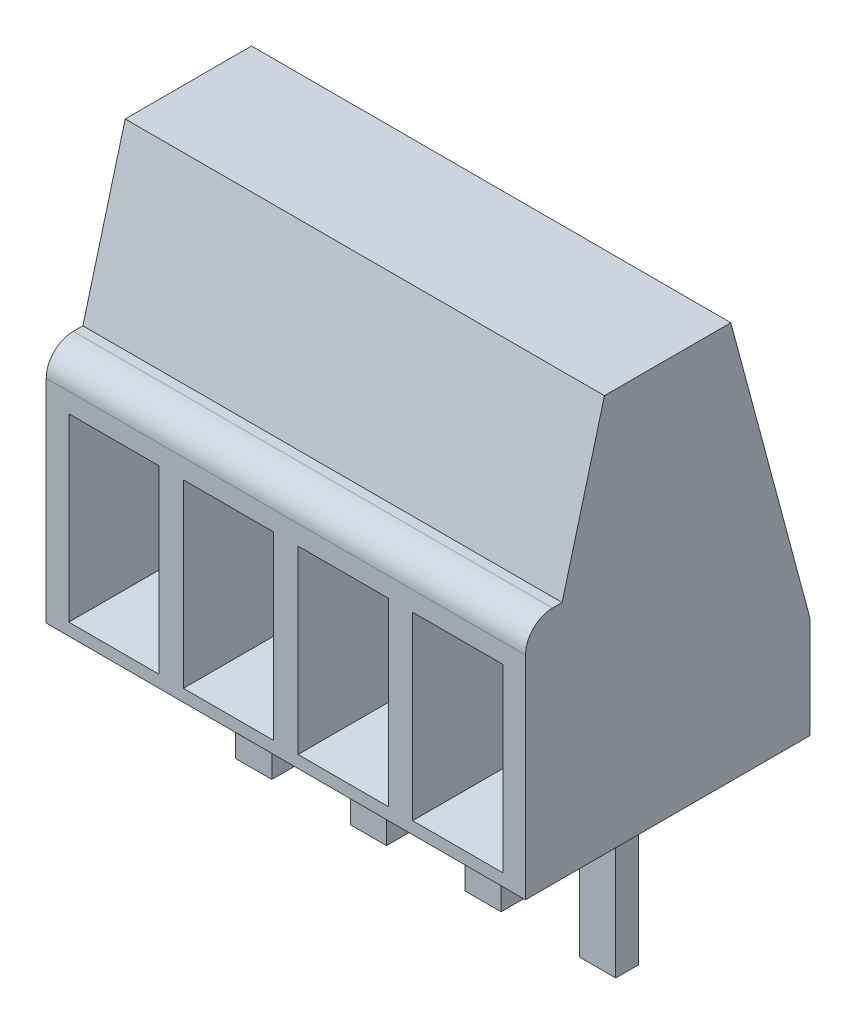
SolidWorks part; units mm, degrees
ref_plane "Front Plane" through (0, 0, 0) normal (0, 0, 1) x (1, 0, 0)
ref_plane "Top Plane" through (0, 0, 0) normal (0, 1, 0) x (1, 0, 0)
ref_plane "Right Plane" through (0, 0, 0) normal (1, 0, 0) x (0, 0, -1)
sketch "Sketch1" plane through (0, 0, 0) normal (0, 1, 0) x (1, 0, 0)
  line L1 (-5.31, -3.15) -> (5.31, -3.15)
  line L2 (-5.31, -3.15) -> (-5.31, 3.15)
  line L3 (-5.31, 3.15) -> (5.31, 3.15)
  line L4 (5.31, -3.15) -> (5.31, 3.15)
  line L5 (-5.31, -3.15) -> (5.31, 3.15) construction
  line L6 (-5.31, 3.15) -> (5.31, -3.15) construction
  point P0 (0, 0)
  dimension "D1" = 10.62
  dimension "D2" = 6.3
extrude "Boss-Extrude1" add sketch "Sketch1" along normal blind 8.8
sketch "Sketch2" plane through (0, 0, 0) normal (0, 1, 0) x (1, 0, 0)
  line L0 (5.31, 3.15) -> (-5.31, 3.15) construction
  line L1 (0.87, -0.05) -> (1.67, -0.05)
  line L2 (0.87, -0.05) -> (0.87, 0.45)
  line L3 (0.87, 0.45) -> (1.67, 0.45)
  line L4 (1.67, -0.05) -> (1.67, 0.45)
  line L5 (0.87, -0.05) -> (1.67, 0.45) construction
  line L6 (0.87, 0.45) -> (1.67, -0.05) construction
  line L7 (3.41, -0.05) -> (4.21, -0.05)
  line L8 (3.41, -0.05) -> (3.41, 0.45)
  line L9 (3.41, 0.45) -> (4.21, 0.45)
  line L10 (4.21, -0.05) -> (4.21, 0.45)
  line L11 (3.41, -0.05) -> (4.21, 0.45) construction
  line L12 (3.41, 0.45) -> (4.21, -0.05) construction
  line L13 (-0.87, -0.05) -> (-1.67, -0.05)
  line L14 (-0.87, -0.05) -> (-0.87, 0.45)
  line L15 (-0.87, 0.45) -> (-1.67, 0.45)
  line L16 (-1.67, -0.05) -> (-1.67, 0.45)
  line L17 (-0.87, -0.05) -> (-1.67, 0.45) construction
  line L18 (-0.87, 0.45) -> (-1.67, -0.05) construction
  line L19 (-3.41, -0.05) -> (-4.21, -0.05)
  line L20 (-3.41, -0.05) -> (-3.41, 0.45)
  line L21 (-3.41, 0.45) -> (-4.21, 0.45)
  line L22 (-4.21, -0.05) -> (-4.21, 0.45)
  line L23 (-3.41, -0.05) -> (-4.21, 0.45) construction
  line L24 (-3.41, 0.45) -> (-4.21, -0.05) construction
  point P0 (1.27, 0.2)
  point P6 (3.81, 0.2)
  point P11 (-1.27, 0.2)
  point P20 (1.27, 0.2)
  point P22 (-3.81, 0.2)
  dimension "D1" = 2.54
  dimension "D2" = 2.54
  dimension "D3" = 0.8
  dimension "D4" = 2.54
  dimension "D5" = 1.27
  dimension "D6" = 0.5
  dimension "D7" = 2.95
extrude "Boss-Extrude2" add sketch "Sketch2" against normal blind 3.6
sketch "Sketch3" plane through (5.31, 0, 0) normal (1, 0, 0) x (0, 0, -1)
  line L1 (-3.15, 8.8) -> (-3.15, 0) construction
  line L2 (-2.55, 5.3) -> (-2.3378, 5.3)
  line L3 (-2.3378, 5.3) -> (-1.4, 8.8)
  line L4 (-3.15, 8.8) -> (3.15, 8.8) construction
  line L5 (-1.4, 8.8) -> (1.4, 8.8)
  line L6 (1.4, 8.8) -> (3.15, 2.2689)
  line L7 (3.15, 8.8) -> (3.15, 0) construction
  line L10 (1.4, 8.8) -> (3.15, 8.8)
  line L11 (3.15, 8.8) -> (3.15, 2.2689)
  line L12 (-3.15, 4.7) -> (-3.15, 8.8)
  line L13 (-3.15, 8.8) -> (-1.4, 8.8)
  line L14 (-3.15, 0) -> (3.15, 0) construction
  arc A0 (-3.15, 4.7) -> (-2.55, 5.3) centre (-2.55, 4.7) cw
  point P18 (0, 8.8)
  line M12 (3.15, 0) -> (3.15, 8.8)
  line M13 (3.15, 8.8) -> (-3.15, 8.8)
  line M14 (-3.15, 8.8) -> (-3.15, 0)
  dimension "D3" = 4.7
  dimension "D1" = 15
  dimension "D2" = 75
  dimension "D4" = 2.8
  dimension "D5" = 5.3
extrude "Cut-Extrude1" cut sketch "Sketch3" against normal up to next contours A0 L2 L3 M14 M13 | L6 M13 M12
sketch "Sketch4" plane through (0, 0, 3.15) normal (0, 0, 1) x (1, 0, 0)
  line L1 (-4.81, 0.2689) -> (-2.81, 0.2689)
  line L2 (-4.81, 0.2689) -> (-4.81, 4.2689)
  line L3 (-4.81, 4.2689) -> (-2.81, 4.2689)
  line L4 (-2.81, 0.2689) -> (-2.81, 4.2689)
  line L5 (-4.81, 0.2689) -> (-2.81, 4.2689) construction
  line L6 (-4.81, 4.2689) -> (-2.81, 0.2689) construction
  line L7 (-2.27, 0.2689) -> (-0.27, 0.2689)
  line L8 (-2.27, 0.2689) -> (-2.27, 4.2689)
  line L9 (-2.27, 4.2689) -> (-0.27, 4.2689)
  line L10 (-0.27, 0.2689) -> (-0.27, 4.2689)
  line L11 (-2.27, 0.2689) -> (-0.27, 4.2689) construction
  line L12 (-2.27, 4.2689) -> (-0.27, 0.2689) construction
  line L13 (2.27, 4.2689) -> (0.27, 4.2689)
  line L14 (2.27, 4.2689) -> (2.27, 0.2689)
  line L15 (2.27, 0.2689) -> (0.27, 0.2689)
  line L16 (0.27, 4.2689) -> (0.27, 0.2689)
  line L17 (2.27, 4.2689) -> (0.27, 0.2689) construction
  line L18 (2.27, 0.2689) -> (0.27, 4.2689) construction
  line L20 (4.81, 4.2689) -> (2.81, 4.2689)
  line L21 (4.81, 4.2689) -> (4.81, 0.2689)
  line L22 (4.81, 0.2689) -> (2.81, 0.2689)
  line L23 (2.81, 4.2689) -> (2.81, 0.2689)
  line L25 (2.81, 4.2689) -> (4.81, 0.2689) construction
  line L26 (-4.21, -3.6) -> (-3.41, -3.6) construction
  line L27 (2.81, 0.2689) -> (4.81, 4.2689) construction
  line L28 (3.41, -3.6) -> (4.21, -3.6) construction
  line L29 (0.87, -3.6) -> (1.67, -3.6) construction
  line L30 (-1.67, -3.6) -> (-0.87, -3.6) construction
  point P0 (-3.81, 2.2689)
  point P5 (-1.27, 2.2689)
  point P10 (1.27, 2.2689)
  point P21 (0, 2.2689)
  point P23 (3.81, -3.6)
  point P24 (3.81, 2.2689)
  point P31 (-3.81, -3.6)
  point P32 (1.27, -3.6)
  point P35 (-1.27, -3.6)
  dimension "D1" = 2
  dimension "D2" = 4
extrude "Cut-Extrude2" cut sketch "Sketch4" against normal blind 3.15 draft 10
